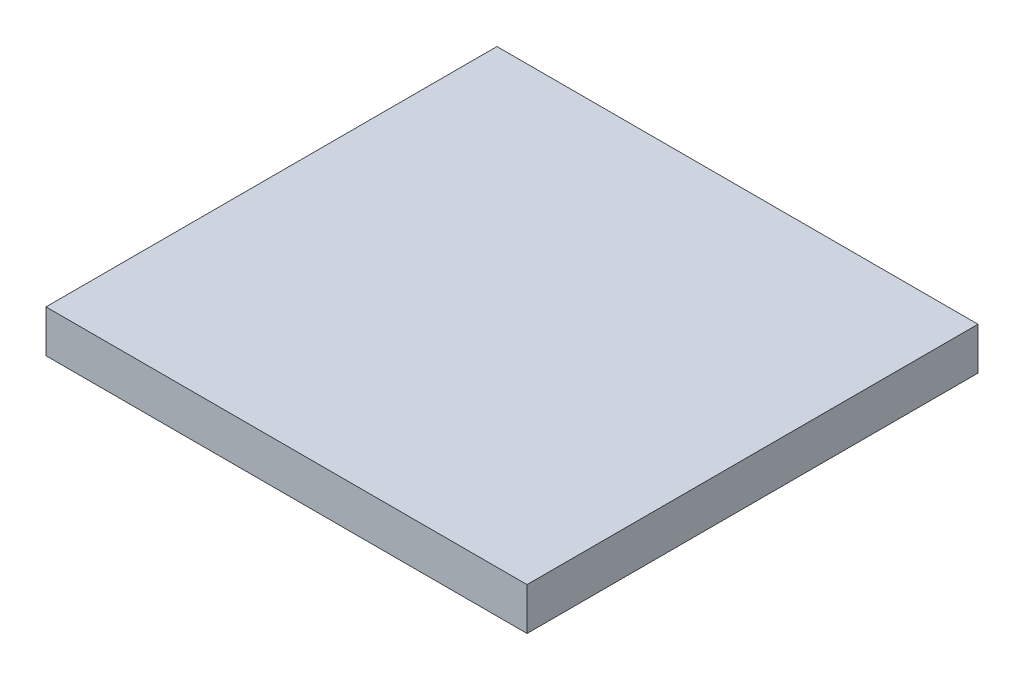
SolidWorks part; units mm, degrees
ref_plane "Plano frontal" through (0, 0, 0) normal (0, 0, 1) x (1, 0, 0)
ref_plane "Plano superior" through (0, 0, 0) normal (0, 1, 0) x (1, 0, 0)
ref_plane "Plano direito" through (0, 0, 0) normal (1, 0, 0) x (0, 0, -1)
sketch "Sketch1" plane through (0, 0, 705.9374) normal (0, 1, 0) x (1, 0, 0)
  line L1 (-23172.0165, -40463.2712) -> (-23399.2314, -40463.2712)
  line L2 (-23172.0165, -40463.2712) -> (-23172.0165, -40676.2851)
  line L3 (-23172.0165, -40676.2851) -> (-23399.2314, -40676.2851)
  line L4 (-23399.2314, -40463.2712) -> (-23399.2314, -40676.2851)
extrude "Boss-Extrude1" add sketch "Sketch1" along normal blind 20 from surface at 5474.8688
